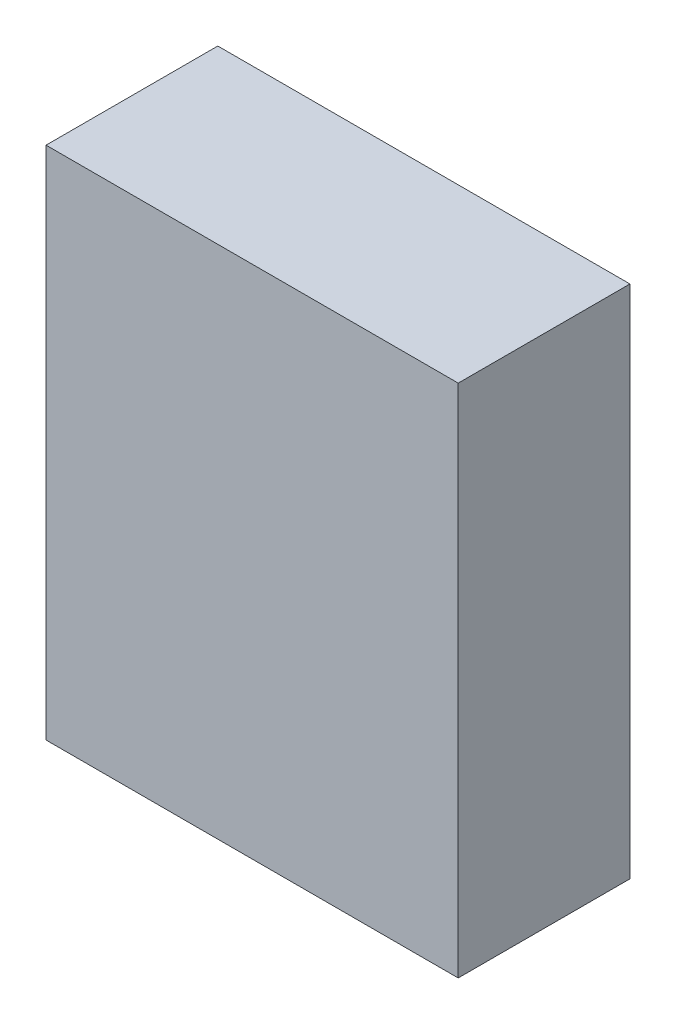
SolidWorks part; units mm, degrees
material "Thornel VCB-20 碳布"
ref_plane "前视基准面" through (0, 0, 0) normal (0, 0, 1) x (1, 0, 0)
ref_plane "上视基准面" through (0, 0, 0) normal (0, 1, 0) x (1, 0, 0)
ref_plane "右视基准面" through (0, 0, 0) normal (1, 0, 0) x (0, 0, -1)
sketch "草图1" plane through (0, 0, 0) normal (0, 0, 1) x (1, 0, 0)
  line L1 (-30, 37.5) -> (30, 37.5)
  line L2 (-30, 37.5) -> (-30, -37.5)
  line L3 (-30, -37.5) -> (30, -37.5)
  line L4 (30, 37.5) -> (30, -37.5)
  line L5 (0, -37.5) -> (0, 37.5) construction
  line L6 (-30, 0) -> (30, 0) construction
  point P0 (0, 0)
  dimension "D1" = 60
  dimension "D2" = 75
extrude "凸台-拉伸1" add sketch "草图1" along normal blind 25
